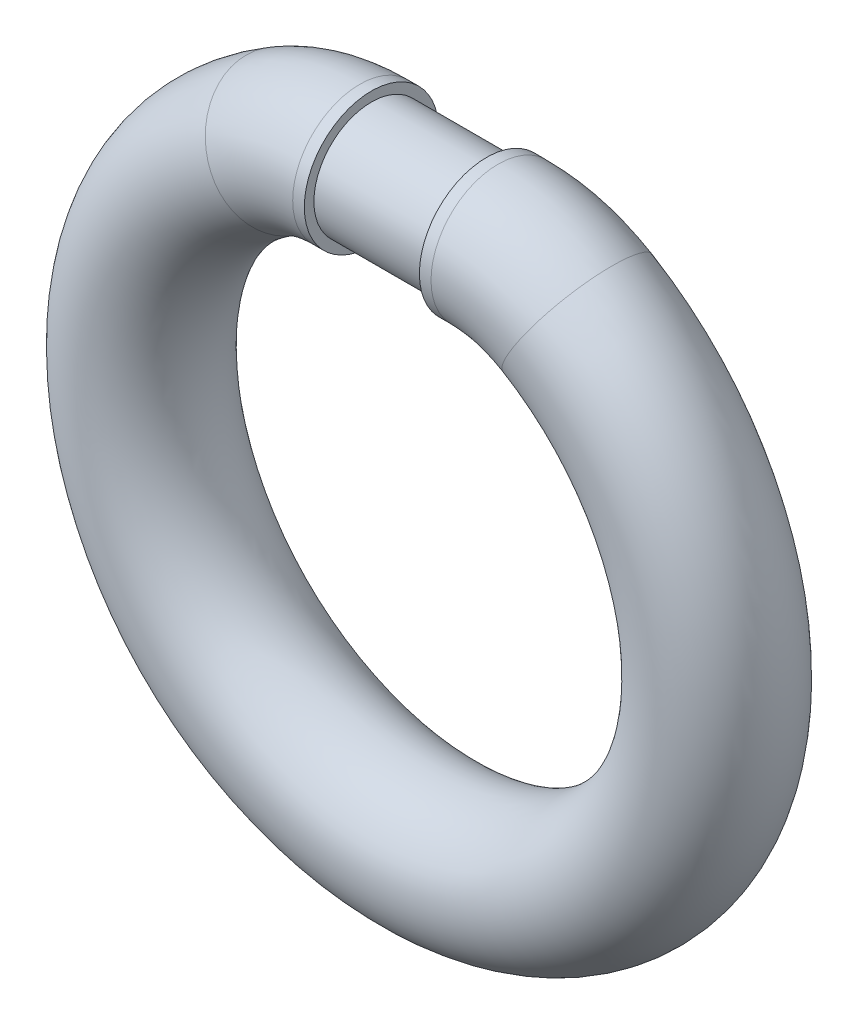
SolidWorks part; units mm, degrees
material "Серое литое железо (SN)"
ref_plane "Спереди" through (0, 0, 0) normal (0, 0, 1) x (1, 0, 0)
ref_plane "Сверху" through (0, 0, 0) normal (0, 1, 0) x (1, 0, 0)
ref_plane "Справа" through (0, 0, 0) normal (1, 0, 0) x (0, 0, -1)
sketch "Эскиз1" plane through (0, 0, 0) normal (0, 0, 1) x (1, 0, 0)
  line L0 (0, 44.7863) -> (0, -27.8632) construction
  line L1 (-50.2564, 0) -> (51.2821, 0) construction
  line L2 (-30, 0) -> (-30, 30)
  line L3 (-30, 30) -> (30, 30)
  line L4 (30, 0) -> (30, 30)
  line L5 (-30, 0) -> (30, 0)
  point P9 (0, 30)
  dimension "D1" = 30
  dimension "D2" = 30
revolve "Повернуть1" add sketch "Эскиз1" angle 360 about L1
sketch "Эскиз2" plane through (0, 0, 0) normal (0, 0, 1) x (1, 0, 0)
  line L0 (0, 32.0253) -> (0, -235.1512) construction
  line L1 (-179.5744, 0) -> (133.5264, 0) construction
  line L2 (-36.0555, 0) -> (-30, 0)
  line L3 (-30, 30) -> (-30, -30) construction
  line L4 (36.0555, 0) -> (30, 0)
  arc A0 (-77.2618, -11.4286) -> (77.2618, -11.4286) centre (0, -140) ccw
  arc A1 (77.2618, -11.4286) -> (36.0555, 0) centre (36.0555, -80) ccw
  arc A2 (-77.2618, -11.4286) -> (-36.0555, 0) centre (-36.0555, -80) cw
  point P15 (53.8516, 0)
  point P18 (-53.8516, 0)
  dimension "D1" = 150
  dimension "D3" = 80
  dimension "D2" = 140
sketch "Эскиз3" plane through (-30, 0, 0) normal (-1, 0, 0) x (0, 0, 1)
  line L0 (-58.227, 0) -> (42.6833, 0) construction
  circle A0 centre (0, 0) radius 35
  dimension "D1" = 70
sweep "По траектории1" add profiles "Эскиз3" path "Эскиз2"
